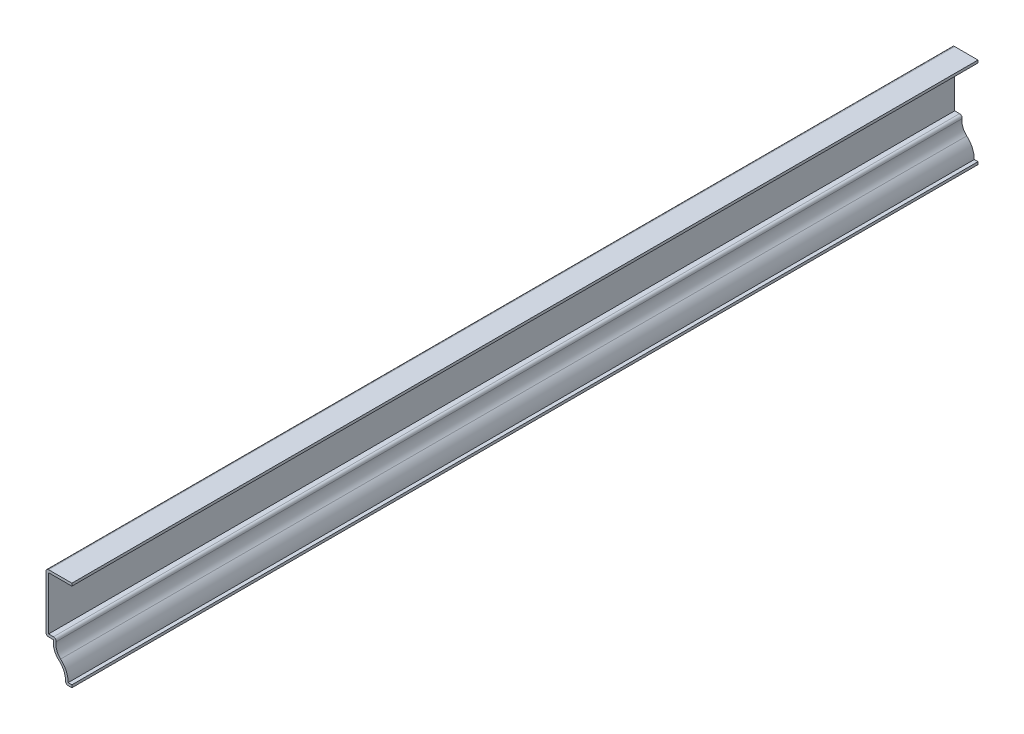
SolidWorks part; units mm, degrees
ref_plane "Front Plane" through (0, 0, 0) normal (0, 0, 1) x (1, 0, 0)
ref_plane "Top Plane" through (0, 0, 0) normal (0, 1, 0) x (1, 0, 0)
ref_plane "Right Plane" through (0, 0, 0) normal (1, 0, 0) x (0, 0, -1)
sketch "Sketch1" plane through (0, 0, 0) normal (0, 0, 1) x (1, 0, 0)
  line L0 (0, 0) -> (-3.175, 0)
  line L1 (-9.0284, 15.875) -> (-12.7, 15.875)
  line L2 (-12.7, 15.875) -> (-12.7, 44.45)
  line L3 (-12.7, 44.45) -> (0, 44.45)
  line L4 (0, 44.45) -> (0, 0) construction
  line L5 (-12.7, 1.27) -> (-0.992, 14.605) construction
  arc A0 (-3.175, 0) -> (-6.36, 8.491) centre (-12.7, 1.27) ccw
  arc A1 (-6.36, 8.491) -> (-9.0284, 15.875) centre (-0.992, 14.605) cw
  point P9 (-6.1878, 7.8239)
  point P11 (-10.2683, 2.4604)
  point P12 (-6.2416, 8.1274)
  point P13 (0, 0)
  dimension "D1" = 44.45
  dimension "D2" = 12.7
  dimension "D3" = 28.575
  dimension "D4" = 3.175
  dimension "D5" = 5.9531
  dimension "D6" = 1.27
  dimension "D7" = 1.27
extrude "Extrude-Thin1" add sketch "Sketch1" against normal blind 444.5 thin
fillet "Fillet1" radius 1.27 4 edges at (-3.175, 0, -222.25) (-12.7, 15.875, -222.25) (-7.371, 17.145, -222.25) (-12.7, 44.45, -222.25)
